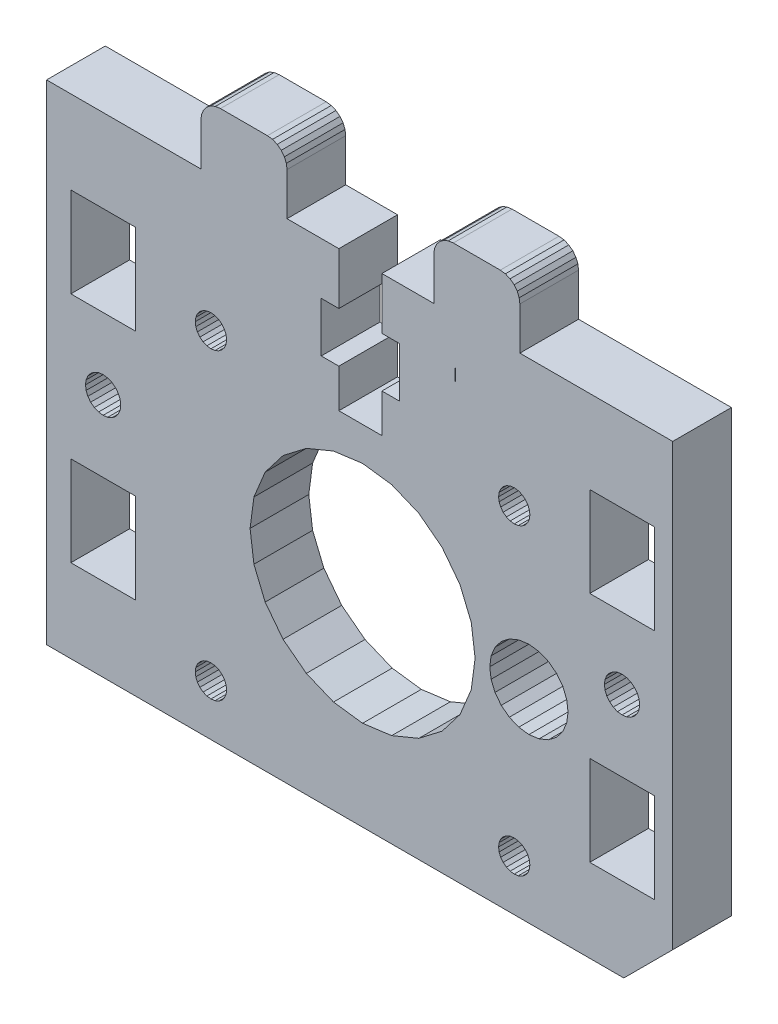
SolidWorks part; units mm, degrees
material "Maple"
ref_plane "Front Plane" through (0, 0, 0) normal (0, 0, 1) x (1, 0, 0)
ref_plane "Top Plane" through (0, 0, 0) normal (0, 1, 0) x (1, 0, 0)
ref_plane "Right Plane" through (0, 0, 0) normal (1, 0, 0) x (0, 0, -1)
sketch "Sketch1" plane through (0, 0, 0) normal (0, 0, 1) x (1, 0, 0)
  line L7432 (314.8926, 118.0571) -> (314.0641, 117.4214)
  line L7433 (315.8573, 118.4567) -> (314.8926, 118.0571)
  line L7434 (297.4676, 143.893) -> (297.4676, 138.593)
  line L7435 (314.0641, 117.4214) -> (313.4285, 116.593)
  line L7436 (313.4285, 116.593) -> (313.0289, 115.6282)
  line L7437 (320.7563, 113.5577) -> (320.8926, 114.593)
  line L7438 (284.3926, 100.693) -> (283.9785, 100.6385)
  line L7439 (301.8676, 133.493) -> (303.6676, 133.493)
  line L7440 (313.4285, 112.593) -> (314.0641, 111.7645)
  line L7441 (331.5926, 98.893) -> (326.5926, 93.893)
  line L7442 (314.8926, 111.1289) -> (315.8573, 110.7293)
  line L7443 (301.8676, 138.593) -> (301.8676, 143.893)
  line L7444 (314.0641, 111.7645) -> (314.8926, 111.1289)
  line L7445 (317.9278, 118.4567) -> (316.8926, 118.593)
  line L7446 (318.8926, 111.1289) -> (319.721, 111.7645)
  line L7447 (313.0289, 113.5577) -> (313.4285, 112.593)
  line L7448 (320.8926, 114.593) -> (320.7563, 115.6282)
  line L7449 (316.8926, 118.593) -> (315.8573, 118.4567)
  line L7450 (313.0289, 115.6282) -> (312.8926, 114.593)
  line L7451 (316.8926, 110.593) -> (317.9278, 110.7293)
  line L7452 (303.6676, 138.593) -> (301.8676, 138.593)
  line L7453 (297.4676, 129.543) -> (301.8676, 129.543)
  line L7454 (307.1676, 143.893) -> (307.1676, 148.243)
  line L7455 (295.6676, 133.493) -> (297.4676, 133.493)
  line L7456 (295.6676, 138.593) -> (295.6676, 133.493)
  line L7457 (301.8676, 129.543) -> (301.8676, 133.493)
  line L7458 (312.8926, 114.593) -> (313.0289, 113.5577)
  line L7459 (318.8926, 118.0571) -> (317.9278, 118.4567)
  line L7460 (311.0007, 111.6166) -> (311.3926, 114.593)
  line L7461 (320.3567, 116.593) -> (319.721, 117.4214)
  line L7462 (297.4676, 133.493) -> (297.4676, 129.543)
  line L7463 (317.9278, 110.7293) -> (318.8926, 111.1289)
  line L7464 (292.1676, 143.893) -> (297.4676, 143.893)
  line L7465 (283.3676, 143.893) -> (283.3676, 148.243)
  line L7466 (331.5926, 143.893) -> (331.5926, 98.893)
  line L7467 (303.6676, 133.493) -> (303.6676, 138.593)
  line L7468 (297.4676, 138.593) -> (295.6676, 138.593)
  line L7469 (315.8067, 131.6384) -> (315.3926, 131.693)
  line L7470 (320.3567, 112.593) -> (320.7563, 113.5577)
  line L7471 (319.721, 111.7645) -> (320.3567, 112.593)
  line L7472 (315.8573, 110.7293) -> (316.8926, 110.593)
  line L7473 (320.7563, 115.6282) -> (320.3567, 116.593)
  line L7474 (301.8676, 143.893) -> (307.1676, 143.893)
  line L7475 (319.721, 117.4214) -> (318.8926, 118.0571)
  line L7476 (307.1676, 148.243) -> (307.2357, 148.7606)
  line L7477 (307.2357, 148.7606) -> (307.4355, 149.243)
  line L7478 (307.4355, 149.243) -> (307.7534, 149.6572)
  line L7479 (307.7534, 149.6572) -> (308.1676, 149.975)
  line L7480 (308.1676, 149.975) -> (308.6499, 150.1748)
  line L7481 (309.1676, 150.243) -> (313.9676, 150.243)
  line L7482 (308.6499, 150.1748) -> (309.1676, 150.243)
  line L7483 (315.9676, 148.243) -> (315.9676, 143.893)
  line L7484 (315.9676, 148.243) -> (315.8994, 148.7606)
  line L7485 (315.8994, 148.7606) -> (315.6996, 149.243)
  line L7486 (315.6996, 149.243) -> (315.3818, 149.6572)
  line L7487 (315.3818, 149.6572) -> (314.9676, 149.975)
  line L7488 (314.9676, 149.975) -> (314.4852, 150.1748)
  line L7489 (314.4852, 150.1748) -> (313.9676, 150.243)
  line L7490 (283.3676, 148.243) -> (283.4357, 148.7606)
  line L7491 (283.4357, 148.7606) -> (283.6355, 149.243)
  line L7492 (283.6355, 149.243) -> (283.9534, 149.6572)
  line L7493 (283.9534, 149.6572) -> (284.3676, 149.975)
  line L7494 (284.3676, 149.975) -> (284.8499, 150.1748)
  line L7495 (285.3676, 150.243) -> (290.1676, 150.243)
  line L7496 (284.8499, 150.1748) -> (285.3676, 150.243)
  line L7497 (292.1676, 148.243) -> (292.1676, 143.893)
  line L7498 (292.1676, 148.243) -> (292.0994, 148.7606)
  line L7499 (292.0994, 148.7606) -> (291.8996, 149.243)
  line L7500 (291.8996, 149.243) -> (291.5818, 149.6572)
  line L7501 (291.5818, 149.6572) -> (291.1676, 149.975)
  line L7502 (291.1676, 149.975) -> (290.6852, 150.1748)
  line L7503 (290.6852, 150.1748) -> (290.1676, 150.243)
  line L7504 (283.9785, 100.6385) -> (283.5926, 100.4786)
  line L7505 (283.5926, 100.4786) -> (283.2612, 100.2243)
  line L7506 (283.2612, 100.2243) -> (283.0069, 99.893)
  line L7507 (283.0069, 99.893) -> (282.8471, 99.5071)
  line L7508 (282.8471, 99.5071) -> (282.7926, 99.093)
  line L7509 (282.7926, 99.093) -> (282.8471, 98.6789)
  line L7510 (282.8471, 98.6789) -> (283.0069, 98.293)
  line L7511 (283.0069, 98.293) -> (283.2612, 97.9616)
  line L7512 (283.2612, 97.9616) -> (283.5926, 97.7073)
  line L7513 (283.5926, 97.7073) -> (283.9785, 97.5475)
  line L7514 (283.9785, 97.5475) -> (284.3926, 97.493)
  line L7515 (284.3926, 97.493) -> (284.8067, 97.5475)
  line L7516 (284.8067, 97.5475) -> (285.1926, 97.7073)
  line L7517 (285.1926, 97.7073) -> (285.524, 97.9616)
  line L7518 (285.524, 97.9616) -> (285.7782, 98.293)
  line L7519 (285.7782, 98.293) -> (285.9381, 98.6789)
  line L7520 (285.9381, 98.6789) -> (285.9926, 99.093)
  line L7521 (285.9926, 99.093) -> (285.9381, 99.5071)
  line L7522 (285.9381, 99.5071) -> (285.7782, 99.893)
  line L7523 (285.7782, 99.893) -> (285.524, 100.2243)
  line L7524 (285.524, 100.2243) -> (285.1926, 100.4786)
  line L7525 (285.1926, 100.4786) -> (284.8067, 100.6385)
  line L7526 (284.8067, 100.6385) -> (284.3926, 100.693)
  line L7527 (311.3926, 114.593) -> (311.0007, 117.5694)
  line L7528 (311.0007, 117.5694) -> (309.8519, 120.343)
  line L7529 (309.8519, 120.343) -> (308.0243, 122.7247)
  line L7530 (308.0243, 122.7247) -> (305.6426, 124.5523)
  line L7531 (305.6426, 124.5523) -> (302.869, 125.7011)
  line L7532 (302.869, 125.7011) -> (299.8926, 126.093)
  line L7533 (299.8926, 126.093) -> (296.9162, 125.7011)
  line L7534 (296.9162, 125.7011) -> (294.1426, 124.5523)
  line L7535 (294.1426, 124.5523) -> (291.7609, 122.7247)
  line L7536 (291.7609, 122.7247) -> (289.9333, 120.343)
  line L7537 (289.9333, 120.343) -> (288.7844, 117.5694)
  line L7538 (288.7844, 117.5694) -> (288.3926, 114.593)
  line L7539 (288.3926, 114.593) -> (288.7844, 111.6166)
  line L7540 (288.7844, 111.6166) -> (289.9333, 108.843)
  line L7541 (289.9333, 108.843) -> (291.7609, 106.4612)
  line L7542 (291.7609, 106.4612) -> (294.1426, 104.6337)
  line L7543 (294.1426, 104.6337) -> (296.9162, 103.4848)
  line L7544 (296.9162, 103.4848) -> (299.8926, 103.093)
  line L7545 (299.8926, 103.093) -> (302.869, 103.4848)
  line L7546 (302.869, 103.4848) -> (305.6426, 104.6337)
  line L7547 (305.6426, 104.6337) -> (308.0243, 106.4612)
  line L7548 (308.0243, 106.4612) -> (309.8519, 108.843)
  line L7549 (309.8519, 108.843) -> (311.0007, 111.6166)
  line L7550 (315.3926, 131.693) -> (314.9785, 131.6384)
  line L7551 (314.9785, 131.6384) -> (314.5926, 131.4786)
  line L7552 (314.5926, 131.4786) -> (314.2612, 131.2243)
  line L7553 (314.2612, 131.2243) -> (314.0069, 130.893)
  line L7554 (314.0069, 130.893) -> (313.8471, 130.5071)
  line L7555 (313.8471, 130.5071) -> (313.7926, 130.093)
  line L7556 (313.7926, 130.093) -> (313.8471, 129.6789)
  line L7557 (313.8471, 129.6789) -> (314.0069, 129.293)
  line L7558 (314.0069, 129.293) -> (314.2612, 128.9616)
  line L7559 (314.2612, 128.9616) -> (314.5926, 128.7073)
  line L7560 (314.5926, 128.7073) -> (314.9785, 128.5475)
  line L7561 (314.9785, 128.5475) -> (315.3926, 128.493)
  line L7562 (315.3926, 128.493) -> (315.8067, 128.5475)
  line L7563 (315.8067, 128.5475) -> (316.1926, 128.7073)
  line L7564 (316.1926, 128.7073) -> (316.5239, 128.9616)
  line L7565 (316.5239, 128.9616) -> (316.7782, 129.293)
  line L7566 (316.7782, 129.293) -> (316.9381, 129.6789)
  line L7567 (316.9381, 129.6789) -> (316.9926, 130.093)
  line L7568 (316.9926, 130.093) -> (316.9381, 130.5071)
  line L7569 (316.9381, 130.5071) -> (316.7782, 130.893)
  line L7570 (316.7782, 130.893) -> (316.5239, 131.2243)
  line L7571 (316.5239, 131.2243) -> (316.1926, 131.4786)
  line L7572 (316.1926, 131.4786) -> (315.8067, 131.6384)
  line L7573 (274.9329, 119.7938) -> (274.6466, 120.167)
  line L7574 (274.6466, 120.167) -> (274.2734, 120.4533)
  line L7575 (274.2734, 120.4533) -> (273.8389, 120.6333)
  line L7576 (273.8389, 120.6333) -> (273.3726, 120.6947)
  line L7577 (273.3726, 120.6947) -> (272.9063, 120.6333)
  line L7578 (272.9063, 120.6333) -> (272.4717, 120.4533)
  line L7579 (272.4717, 120.4533) -> (272.0986, 120.167)
  line L7580 (272.0986, 120.167) -> (271.8122, 119.7938)
  line L7581 (271.8122, 119.7938) -> (271.6323, 119.3593)
  line L7582 (271.6323, 119.3593) -> (271.5709, 118.893)
  line L7583 (271.5709, 118.893) -> (271.6323, 118.4267)
  line L7584 (271.6323, 118.4267) -> (271.8122, 117.9921)
  line L7585 (271.8122, 117.9921) -> (272.0986, 117.619)
  line L7586 (272.0986, 117.619) -> (272.4717, 117.3326)
  line L7587 (272.4717, 117.3326) -> (272.9063, 117.1526)
  line L7588 (272.9063, 117.1526) -> (273.3726, 117.0912)
  line L7589 (273.3726, 117.0912) -> (273.8389, 117.1526)
  line L7590 (273.8389, 117.1526) -> (274.2734, 117.3326)
  line L7591 (274.2734, 117.3326) -> (274.6466, 117.619)
  line L7592 (274.6466, 117.619) -> (274.9329, 117.9921)
  line L7593 (274.9329, 117.9921) -> (275.1129, 118.4267)
  line L7594 (275.1129, 118.4267) -> (275.1743, 118.893)
  line L7595 (275.1743, 118.893) -> (275.1129, 119.3593)
  line L7596 (275.1129, 119.3593) -> (274.9329, 119.7938)
  line L7597 (324.8522, 119.7938) -> (324.6722, 119.3593)
  line L7598 (324.6722, 119.3593) -> (324.6108, 118.893)
  line L7599 (324.6108, 118.893) -> (324.6722, 118.4267)
  line L7600 (324.6722, 118.4267) -> (324.8522, 117.9921)
  line L7601 (324.8522, 117.9921) -> (325.1386, 117.619)
  line L7602 (325.1386, 117.619) -> (325.5117, 117.3326)
  line L7603 (325.5117, 117.3326) -> (325.9462, 117.1526)
  line L7604 (325.9462, 117.1526) -> (326.4126, 117.0912)
  line L7605 (326.4126, 117.0912) -> (326.8789, 117.1526)
  line L7606 (326.8789, 117.1526) -> (327.3134, 117.3326)
  line L7607 (327.3134, 117.3326) -> (327.6866, 117.619)
  line L7608 (327.6866, 117.619) -> (327.9729, 117.9921)
  line L7609 (327.9729, 117.9921) -> (328.1529, 118.4267)
  line L7610 (328.1529, 118.4267) -> (328.2143, 118.893)
  line L7611 (328.2143, 118.893) -> (328.1529, 119.3593)
  line L7612 (328.1529, 119.3593) -> (327.9729, 119.7938)
  line L7613 (327.9729, 119.7938) -> (327.6866, 120.167)
  line L7614 (327.6866, 120.167) -> (327.3134, 120.4533)
  line L7615 (327.3134, 120.4533) -> (326.8789, 120.6333)
  line L7616 (326.8789, 120.6333) -> (326.4126, 120.6947)
  line L7617 (326.4126, 120.6947) -> (325.9462, 120.6333)
  line L7618 (325.9462, 120.6333) -> (325.5117, 120.4533)
  line L7619 (325.5117, 120.4533) -> (325.1386, 120.167)
  line L7620 (325.1386, 120.167) -> (324.8522, 119.7938)
  line L7621 (285.7782, 130.893) -> (285.524, 131.2243)
  line L7622 (285.524, 131.2243) -> (285.1926, 131.4786)
  line L7623 (285.1926, 131.4786) -> (284.8067, 131.6384)
  line L7624 (284.8067, 131.6384) -> (284.3926, 131.693)
  line L7625 (284.3926, 131.693) -> (283.9785, 131.6384)
  line L7626 (283.9785, 131.6384) -> (283.5926, 131.4786)
  line L7627 (283.5926, 131.4786) -> (283.2612, 131.2243)
  line L7628 (283.2612, 131.2243) -> (283.0069, 130.893)
  line L7629 (283.0069, 130.893) -> (282.8471, 130.5071)
  line L7630 (282.8471, 130.5071) -> (282.7926, 130.093)
  line L7631 (282.7926, 130.093) -> (282.8471, 129.6789)
  line L7632 (282.8471, 129.6789) -> (283.0069, 129.293)
  line L7633 (283.0069, 129.293) -> (283.2612, 128.9616)
  line L7634 (283.2612, 128.9616) -> (283.5926, 128.7073)
  line L7635 (283.5926, 128.7073) -> (283.9785, 128.5475)
  line L7636 (283.9785, 128.5475) -> (284.3926, 128.493)
  line L7637 (284.3926, 128.493) -> (284.8067, 128.5475)
  line L7638 (284.8067, 128.5475) -> (285.1926, 128.7073)
  line L7639 (285.1926, 128.7073) -> (285.524, 128.9616)
  line L7640 (285.524, 128.9616) -> (285.7782, 129.293)
  line L7641 (285.7782, 129.293) -> (285.9381, 129.6789)
  line L7642 (285.9381, 129.6789) -> (285.9926, 130.093)
  line L7643 (285.9926, 130.093) -> (285.9381, 130.5071)
  line L7644 (285.9381, 130.5071) -> (285.7782, 130.893)
  line L7645 (276.6726, 135.393) -> (270.0726, 135.393)
  line L7646 (270.0726, 135.393) -> (270.0726, 126.193)
  line L7647 (270.0726, 126.193) -> (276.6726, 126.193)
  line L7648 (276.6726, 126.193) -> (276.6726, 135.393)
  line L7649 (315.8067, 97.5475) -> (316.1926, 97.7073)
  line L7650 (316.1926, 97.7073) -> (316.5239, 97.9616)
  line L7651 (316.5239, 97.9616) -> (316.7782, 98.293)
  line L7652 (316.7782, 98.293) -> (316.9381, 98.6789)
  line L7653 (316.9381, 98.6789) -> (316.9926, 99.093)
  line L7654 (316.9926, 99.093) -> (316.9381, 99.5071)
  line L7655 (316.9381, 99.5071) -> (316.7782, 99.893)
  line L7656 (316.7782, 99.893) -> (316.5239, 100.2243)
  line L7657 (316.5239, 100.2243) -> (316.1926, 100.4786)
  line L7658 (316.1926, 100.4786) -> (315.8067, 100.6385)
  line L7659 (315.8067, 100.6385) -> (315.3926, 100.693)
  line L7660 (315.3926, 100.693) -> (314.9785, 100.6385)
  line L7661 (314.9785, 100.6385) -> (314.5926, 100.4786)
  line L7662 (314.5926, 100.4786) -> (314.2612, 100.2243)
  line L7663 (314.2612, 100.2243) -> (314.0069, 99.893)
  line L7664 (314.0069, 99.893) -> (313.8471, 99.5071)
  line L7665 (313.8471, 99.5071) -> (313.7926, 99.093)
  line L7666 (313.7926, 99.093) -> (313.8471, 98.6789)
  line L7667 (313.8471, 98.6789) -> (314.0069, 98.293)
  line L7668 (314.0069, 98.293) -> (314.2612, 97.9616)
  line L7669 (314.2612, 97.9616) -> (314.5926, 97.7073)
  line L7670 (314.5926, 97.7073) -> (314.9785, 97.5475)
  line L7671 (314.9785, 97.5475) -> (315.3926, 97.493)
  line L7672 (315.3926, 97.493) -> (315.8067, 97.5475)
  line L7673 (270.0726, 111.593) -> (270.0726, 102.393)
  line L7674 (270.0726, 102.393) -> (276.6726, 102.393)
  line L7675 (276.6726, 102.393) -> (276.6726, 111.593)
  line L7676 (276.6726, 111.593) -> (270.0726, 111.593)
  line L7677 (323.1126, 126.193) -> (329.7126, 126.193)
  line L7678 (329.7126, 126.193) -> (329.7126, 135.393)
  line L7679 (329.7126, 135.393) -> (323.1126, 135.393)
  line L7680 (323.1126, 135.393) -> (323.1126, 126.193)
  line L7681 (329.7126, 111.593) -> (323.1126, 111.593)
  line L7682 (323.1126, 111.593) -> (323.1126, 102.393)
  line L7683 (323.1126, 102.393) -> (329.7126, 102.393)
  line L7684 (329.7126, 102.393) -> (329.7126, 111.593)
  line L8448 (267.5926, 143.893) -> (283.3676, 143.893)
  line L8449 (267.5926, 93.893) -> (267.5926, 143.893)
  line L8450 (315.9676, 143.893) -> (331.5926, 143.893)
  line L8451 (267.5926, 93.893) -> (326.5926, 93.893)
  line L9668 (309.3581, 139.2404) -> (309.3782, 139.3365)
  line L9669 (309.3782, 139.3365) -> (309.4385, 139.4253)
  line L9670 (309.4385, 139.4253) -> (309.6797, 139.5806)
  line L9671 (309.6797, 139.5806) -> (310.041, 139.686)
  line L9672 (310.041, 139.686) -> (310.482, 139.7211)
  line L9673 (310.482, 139.7211) -> (310.923, 139.686)
  line L9674 (310.923, 139.686) -> (311.2844, 139.5806)
  line L9675 (311.2844, 139.5806) -> (311.5255, 139.4253)
  line L9676 (311.5255, 139.4253) -> (311.5858, 139.3365)
  line L9677 (311.5858, 139.3365) -> (311.6059, 139.2404)
  line L9678 (311.6059, 139.2404) -> (311.6059, 135.8939)
  line L9679 (311.6059, 135.8939) -> (311.5858, 135.7977)
  line L9680 (311.5858, 135.7977) -> (311.5255, 135.709)
  line L9681 (311.5255, 135.709) -> (311.2844, 135.5537)
  line L9682 (311.2844, 135.5537) -> (310.923, 135.4483)
  line L9683 (310.923, 135.4483) -> (310.482, 135.4132)
  line L9684 (310.482, 135.4132) -> (310.041, 135.4483)
  line L9685 (310.041, 135.4483) -> (309.6797, 135.5537)
  line L9686 (309.6797, 135.5537) -> (309.4385, 135.709)
  line L9687 (309.4385, 135.709) -> (309.3782, 135.7977)
  line L9688 (309.3782, 135.7977) -> (309.3581, 135.8939)
  line L9689 (309.3581, 135.8939) -> (309.3581, 136.1999)
  line L9690 (309.3581, 136.1999) -> (309.3581, 135.8939)
  line L9691 (309.3581, 135.8939) -> (309.3782, 135.7977)
  line L9692 (309.3782, 135.7977) -> (309.4385, 135.709)
  line L9693 (309.4385, 135.709) -> (309.6797, 135.5537)
  line L9694 (309.6797, 135.5537) -> (310.041, 135.4483)
  line L9695 (310.041, 135.4483) -> (310.482, 135.4132)
  line L9696 (310.482, 135.4132) -> (310.923, 135.4483)
  line L9697 (310.923, 135.4483) -> (311.2844, 135.5537)
  line L9698 (311.2844, 135.5537) -> (311.5255, 135.709)
  line L9699 (311.5255, 135.709) -> (311.5858, 135.7977)
  line L9700 (311.5858, 135.7977) -> (311.6059, 135.8939)
  line L9701 (311.6059, 135.8939) -> (311.6059, 139.2404)
  line L9702 (311.6059, 139.2404) -> (311.5858, 139.3365)
  line L9703 (311.5858, 139.3365) -> (311.5255, 139.4253)
  line L9704 (311.5255, 139.4253) -> (311.2844, 139.5806)
  line L9705 (311.2844, 139.5806) -> (310.923, 139.686)
  line L9706 (310.923, 139.686) -> (310.482, 139.7211)
  line L9707 (310.482, 139.7211) -> (310.041, 139.686)
  line L9708 (310.041, 139.686) -> (309.6797, 139.5806)
  line L9709 (309.6797, 139.5806) -> (309.4385, 139.4253)
  line L9710 (309.4385, 139.4253) -> (309.3782, 139.3365)
  line L9711 (309.3782, 139.3365) -> (309.3581, 137.5671)
  line L9712 (309.3581, 137.5671) -> (310.4695, 137.5671)
  line L9713 (310.4695, 137.5671) -> (309.3581, 137.5671)
  line L9714 (309.3581, 137.5671) -> (309.3581, 139.2404)
extrude "Boss-Extrude1" add sketch "Sketch1" along normal blind 6 contours L8449 L8451 L7441 L7466 L8450 L7483 L7484 L7485 L7486 L7487 L7488 L7489 L7481 L7482 L7480 L7479 L7478 L7477 L7476 L7454 L7474 L7443 L7452 L7467 L7439 L7457 L7453 L7462 L7455 L7456 L7468 L7434 L7464 L7497 L7498 L7499 L7500 L7501 L7502 L7503 L7495 L7496 L7494 L7493 L7492 L7491 L7490 L7465 L8448 L7684
